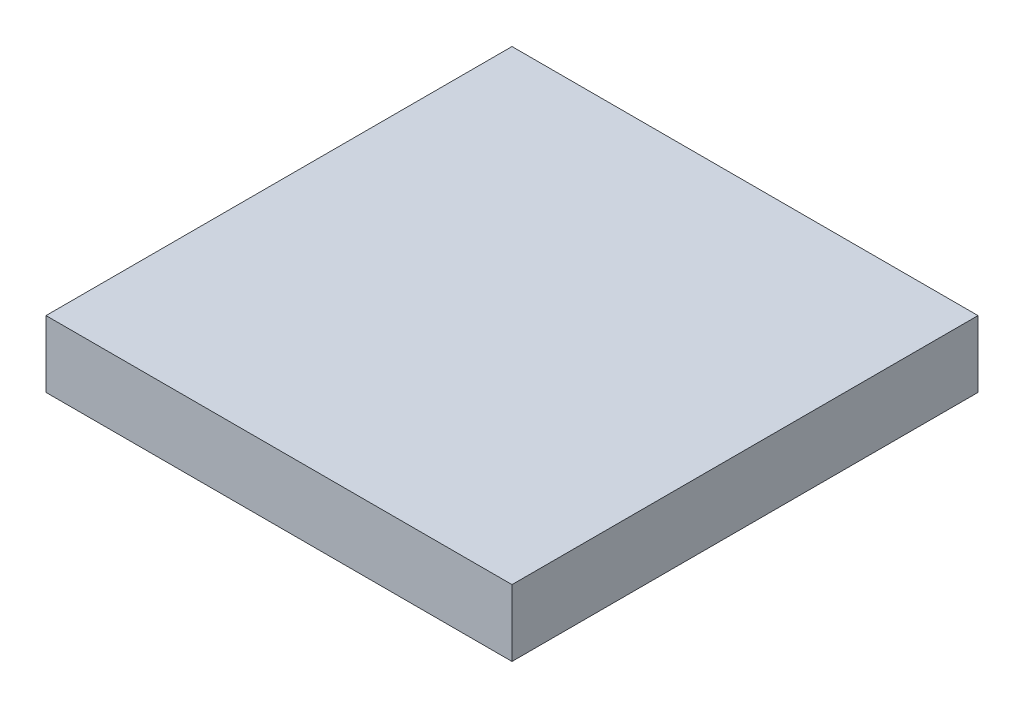
SolidWorks part; units mm, degrees
ref_plane "Front Plane" through (0, 0, 0) normal (0, 0, 1) x (1, 0, 0)
ref_plane "Top Plane" through (0, 0, 0) normal (0, 1, 0) x (1, 0, 0)
ref_plane "Right Plane" through (0, 0, 0) normal (1, 0, 0) x (0, 0, -1)
sketch "Sketch1" plane through (0, 0, 0) normal (0, 1, 0) x (1, 0, 0)
  line L1 (-89.7427, -54.4575) -> (260.2573, -54.4575)
  line L2 (-89.7427, -54.4575) -> (-89.7427, 295.5425)
  line L3 (-89.7427, 295.5425) -> (260.2573, 295.5425)
  line L4 (260.2573, -54.4575) -> (260.2573, 295.5425)
extrude "Boss-Extrude1" add sketch "Sketch1" against normal blind 50
